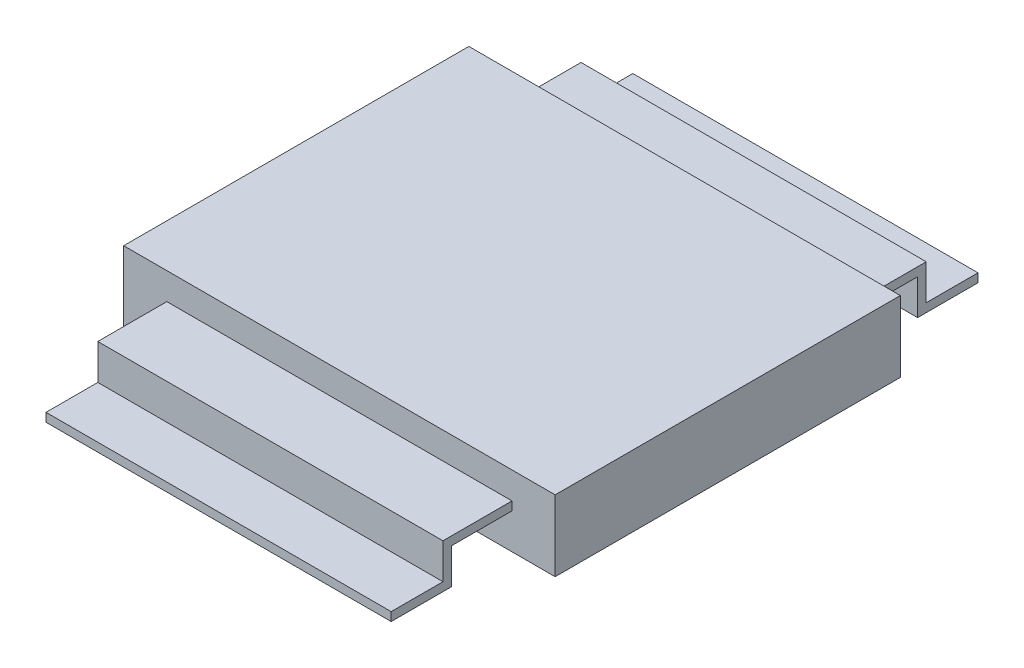
SolidWorks part; units mm, degrees
ref_plane "Front Plane" through (0, 0, 0) normal (0, 0, 1) x (1, 0, 0)
ref_plane "Top Plane" through (0, 0, 0) normal (0, 1, 0) x (1, 0, 0)
ref_plane "Right Plane" through (0, 0, 0) normal (1, 0, 0) x (0, 0, -1)
sketch "Sketch1" plane through (0, 0, 0) normal (1, 0, 0) x (0, 0, -1)
  line L1 (-2.54, 1.044) -> (2.54, 1.044)
  line L2 (-2.54, 1.044) -> (-2.54, 0)
  line L3 (-2.54, 0) -> (2.54, 0)
  line L4 (2.54, 1.044) -> (2.54, 0)
  point P4 (0, 0)
  dimension "D1" = 1.044
  dimension "D2" = 5.08
extrude "Boss-Extrude1" add sketch "Sketch1" along normal mid plane 6.35
sketch "Sketch2" plane through (0, 0, 0) normal (1, 0, 0) x (0, 0, -1)
  line L0 (-2.54, 0.522) -> (-3.429, 0.522)
  line L1 (-2.54, 1.044) -> (-2.54, 0) construction
  line L2 (-3.429, 0.522) -> (-3.429, 0)
  line L3 (-3.429, 0) -> (-4.318, 0)
  dimension "D1" = 1.778
extrude "Extrude-Thin1" add sketch "Sketch2" along normal mid plane 5.08 thin
mirror "Mirror1" about plane through (0, 0, 0) normal (0, 0, 1) of "Extrude-Thin1"
